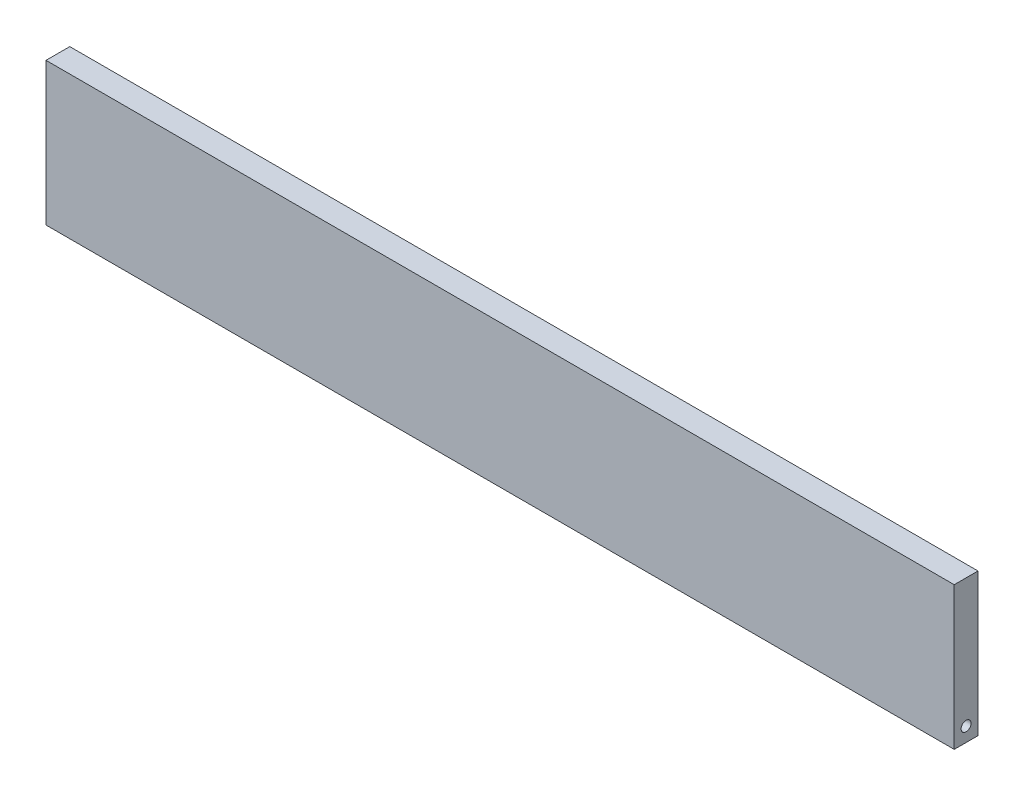
SolidWorks part; units mm, degrees
ref_plane "Plan de face" through (0, 0, 0) normal (0, 0, 1) x (1, 0, 0)
ref_plane "Plan de dessus" through (0, 0, 0) normal (0, 1, 0) x (1, 0, 0)
ref_plane "Plan de droite" through (0, 0, 0) normal (1, 0, 0) x (0, 0, -1)
sketch "Esquisse1" plane through (0, 0, 0) normal (0, 0, 1) x (1, 0, 0)
  line L1 (-88.3428, -16.3742) -> (102.6572, -16.3742)
  line L2 (-88.3428, -16.3742) -> (-88.3428, -46.3742)
  line L3 (-88.3428, -46.3742) -> (102.6572, -46.3742)
  line L4 (102.6572, -16.3742) -> (102.6572, -46.3742)
extrude "Boss.-Extru.1" add sketch "Esquisse1" along normal blind 5
sketch "Esquisse3" plane through (102.6572, 0, 0) normal (1, 0, 0) x (0, 0, -1)
  line L0 (-5, -46.3742) -> (-5, -16.3742) construction
  line L1 (-5, -46.3742) -> (0, -46.3742) construction
  circle A0 centre (-2.5, -43.3742) radius 1.05
  dimension "D1" = 2.5
  dimension "D2" = 3
extrude "Enlèv. mat.-Extru.5" cut sketch "Esquisse3" against normal blind 10
pattern_linear "Répétition linéaire1" count 2 spacing 181 along (-1, 0, 0) of "Enlèv. mat.-Extru.5"
